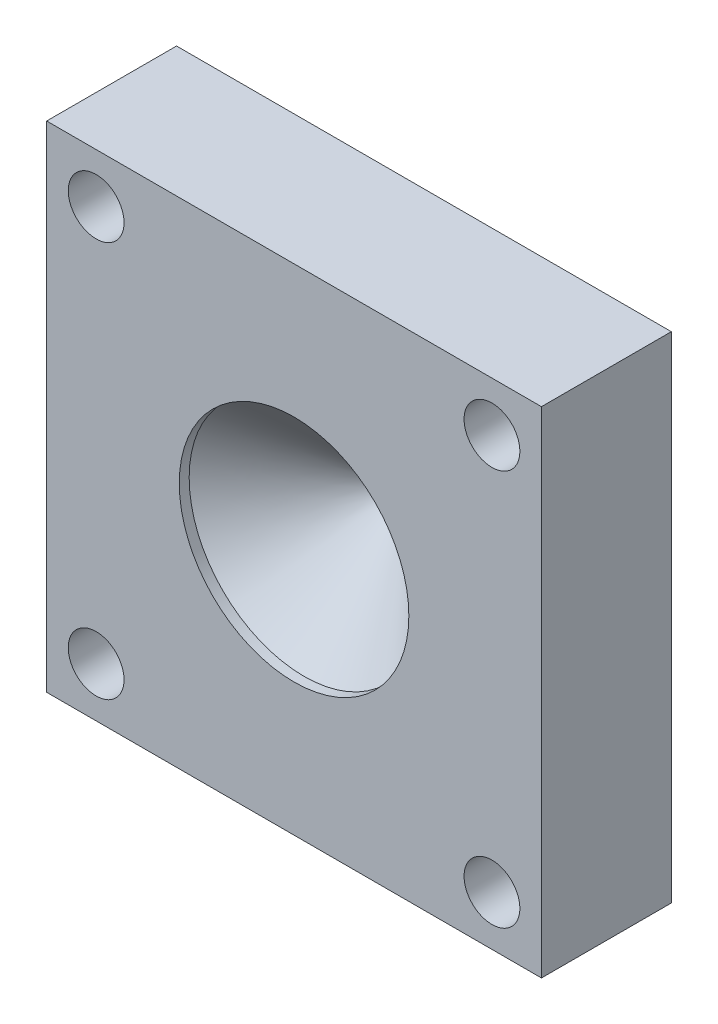
SolidWorks part; units mm, degrees
ref_plane "Front Plane" through (0, 0, 0) normal (0, 0, 1) x (1, 0, 0)
ref_plane "Top Plane" through (0, 0, 0) normal (0, 1, 0) x (1, 0, 0)
ref_plane "Right Plane" through (0, 0, 0) normal (1, 0, 0) x (0, 0, -1)
sketch "Sketch1" plane through (0, 0, 0) normal (0, 0, 1) x (1, 0, 0)
  line L1 (31.75, -31.75) -> (-31.75, -31.75)
  line L2 (31.75, -31.75) -> (31.75, 31.75)
  line L3 (31.75, 31.75) -> (-31.75, 31.75)
  line L4 (-31.75, -31.75) -> (-31.75, 31.75)
  line L5 (31.75, -31.75) -> (-31.75, 31.75) construction
  line L6 (31.75, 31.75) -> (-31.75, -31.75) construction
  circle A0 centre (0, 0) radius 0.7937
  circle A1 centre (-25.4, 25.4) radius 3.5814
  circle A2 centre (25.4, 25.4) radius 3.5814
  circle A3 centre (25.4, -25.4) radius 3.5814
  circle A4 centre (-25.4, -25.4) radius 3.5814
  point P0 (0, 0)
  dimension "D3" = 1.5875
  dimension "D4" = 7.1628
  dimension "D1" = 63.5
  dimension "D2" = 63.5
  dimension "D5" = 25.4
  dimension "D6" = 25.4
  dimension "D7" = 4
extrude "Boss-Extrude1" add sketch "Sketch1" along normal blind 16.6687 contours L2 L1 L4 L3
sketch "Sketch2" plane through (0, 0, 16.6687) normal (0, 0, 1) x (1, 0, 0)
  circle A0 centre (0, 0) radius 14.732
  dimension "D1" = 29.464
extrude "Cut-Extrude1" cut sketch "Sketch2" against normal blind 1.27 contours A0
sketch "Sketch3" plane through (-31.75, 0, 0) normal (-1, 0, 0) x (0, 0, 1)
  line L0 (16.6687, 31.75) -> (0, 31.75) construction
  line L1 (16.6687, -31.75) -> (0, -31.75) construction
  circle A0 centre (8.2521, 11.1125) radius 4.8275
  circle A1 centre (8.2521, 0) radius 3.1541
  circle A2 centre (8.2521, -11.1125) radius 4.4938
  dimension "D1" = 20.6375
  dimension "D2" = 31.75
  dimension "D3" = 20.6375
extrude "Cartidge heater (??? depth)" cut sketch "Sketch3" against normal blind 12.7
sketch "Sketch4" plane through (0, 0, 15.3987) normal (0, 0, 1) x (1, 0, 0)
  circle A0 centre (0, 0) radius 14.732
  dimension "D1" = 29.464
extrude "Cut-Extrude3" cut sketch "Sketch4" against normal blind 12.7 draft 47.5
